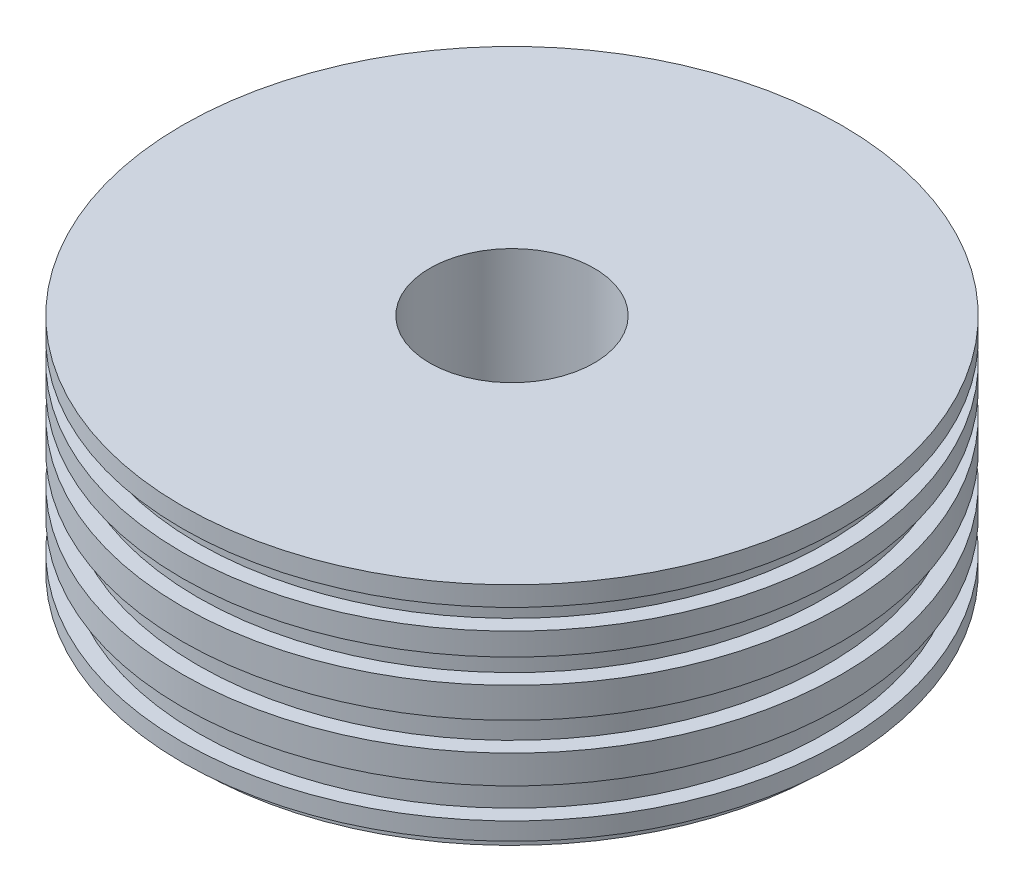
SolidWorks part; units mm, degrees
ref_plane "Alzado" through (0, 0, 0) normal (0, 0, 1) x (1, 0, 0)
ref_plane "Planta" through (0, 0, 0) normal (0, 1, 0) x (1, 0, 0)
ref_plane "Vista lateral" through (0, 0, 0) normal (1, 0, 0) x (0, 0, -1)
sketch "Croquis1" plane through (0, 0, 0) normal (0, 0, 1) x (1, 0, 0)
  line L0 (0, 53.5469) -> (0, -53.0667) construction
  line L1 (40.3403, -53.0667) -> (154.1575, -53.0667)
  line L2 (154.1575, -53.0667) -> (154.1575, -45.8631)
  line L3 (154.1575, -45.8631) -> (161.8414, -45.8631)
  line L4 (161.8414, -45.8631) -> (161.8414, -37.2187)
  line L5 (161.8414, -37.2187) -> (154.1575, -37.2187)
  line L6 (154.1575, -37.2187) -> (154.1575, -22.3312)
  line L7 (154.1575, -22.3312) -> (161.8414, -22.3312)
  line L8 (161.8414, -22.3312) -> (161.8414, -8.4042)
  line L9 (161.8414, -8.4042) -> (154.1575, -8.4042)
  line L10 (154.1575, -8.4042) -> (154.1575, 5.5228)
  line L11 (154.1575, 5.5228) -> (161.8414, 5.5228)
  line L12 (161.8414, 5.5228) -> (161.8414, 20.4103)
  line L13 (161.8414, 20.4103) -> (154.1575, 20.4103)
  line L14 (154.1575, 20.4103) -> (154.1575, 32.4163)
  line L15 (154.1575, 32.4163) -> (161.8414, 32.4163)
  line L16 (161.8414, 32.4163) -> (161.8414, 43.4619)
  line L17 (161.8414, 43.4619) -> (154.1575, 43.4619)
  line L18 (154.1575, 43.4619) -> (154.1575, 53.5469)
  line L19 (154.1575, 53.5469) -> (161.8414, 53.5469)
  line L20 (161.8414, 53.5469) -> (161.8414, 63.1518)
  line L21 (161.8414, 63.1518) -> (40.3403, 63.1518)
  line L22 (40.3403, 63.1518) -> (40.3403, -53.0667)
revolve "Revolución1" add sketch "Croquis1" angle 360 about L0
